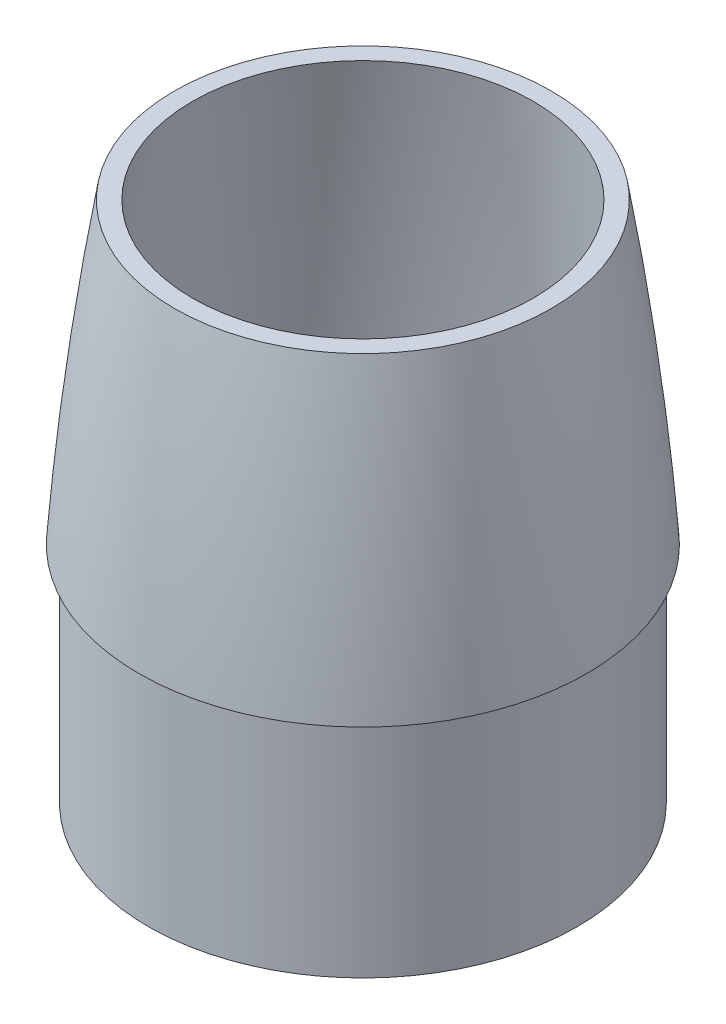
SolidWorks part; units mm, degrees
material "PVB"
ref_plane "Front Plane" through (0, 0, 0) normal (0, 0, 1) x (1, 0, 0)
ref_plane "Top Plane" through (0, 0, 0) normal (0, 1, 0) x (1, 0, 0)
ref_plane "Right Plane" through (0, 0, 0) normal (1, 0, 0) x (0, 0, -1)
sketch "Sketch2" plane through (0, 0, 0) normal (0, 0, 1) x (1, 0, 0)
  line L0 (0, 0) -> (0, 330.2) construction
  line L1 (-76.2, 0) -> (-69.85, 0)
  line L2 (0, 330.2) -> (0, 325.12)
  arc A0 (0, 330.2) -> (-76.2, 0) centre (1014.3906, -77.7824) ccw
  arc A1 (0, 325.12) -> (-69.85, 0) centre (1133.5772, -88.4854) ccw
  dimension "D1" = 330.2
  dimension "D2" = 5.08
  dimension "D3" = 76.2
  dimension "D4" = 6.35
revolve "Revolve1" add sketch "Sketch2" angle 360 about L2
ref_plane "Plane2" through (0, 381, 0) normal (0, 1, 0) x (1, 0, 0)
sketch "Sketch7" plane through (0, 381, 0) normal (0, 1, 0) x (1, 0, 0)
  circle A0 centre (0, 0) radius 317.5
  dimension "D1" = 635
extrude "Cut-Extrude2" cut sketch "Sketch7" against normal blind 279.4
sketch "Sketch8" plane through (0, 0, 0) normal (0, -1, 0) x (1, 0, 0)
  circle A0 centre (0, 0) radius 69.85
  circle A1 centre (0, 0) radius 73.025
  dimension "D1" = 146.05
extrude "Boss-Extrude1" add sketch "Sketch8" along normal blind 76.2
